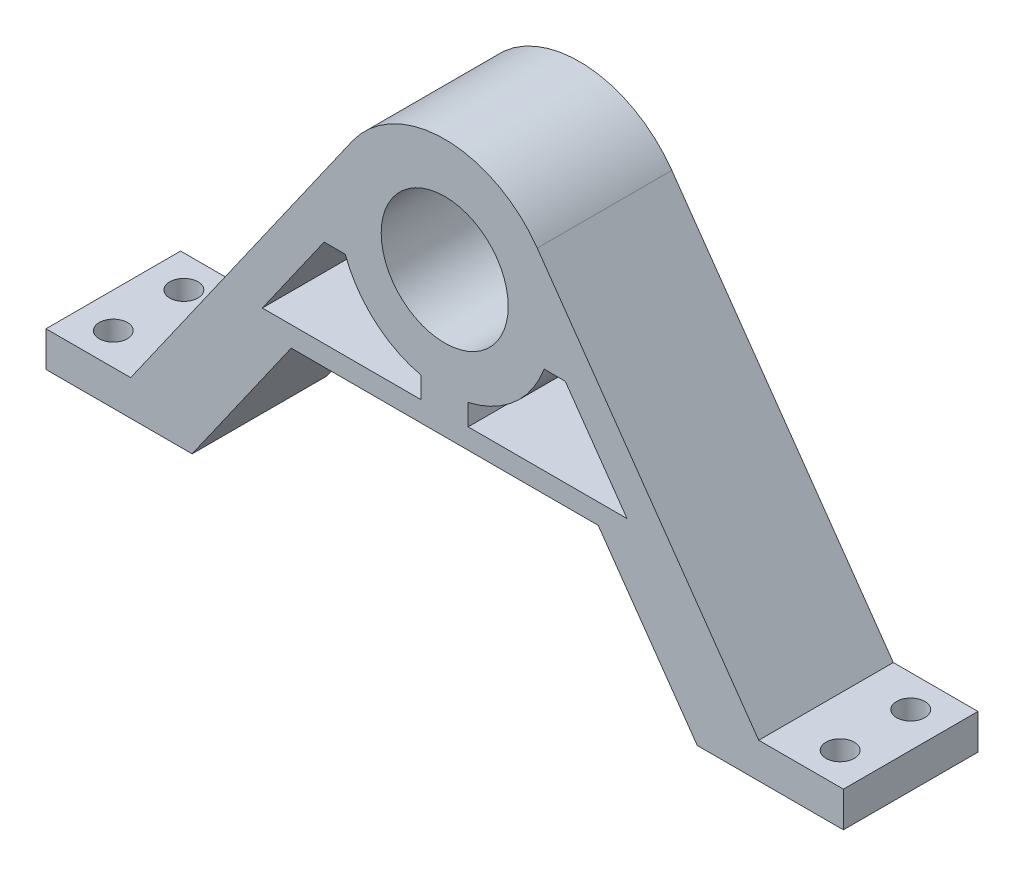
SolidWorks part; units mm, degrees
ref_plane "Plan de face" through (0, 0, 0) normal (0, 0, 1) x (1, 0, 0)
ref_plane "Plan de dessus" through (0, 0, 0) normal (0, 1, 0) x (1, 0, 0)
ref_plane "Plan de droite" through (0, 0, 0) normal (1, 0, 0) x (0, 0, -1)
sketch "Esquisse1" plane through (0, 0, 0) normal (0, 0, 1) x (1, 0, 0)
  line L0 (0, 0) -> (0, 20.2323) construction
  line L2 (-56.5, 0) -> (-56.5, 5)
  line L3 (-56.5, 5) -> (-44.5, 5)
  line L4 (-44.5, 5) -> (-44.5, 64.0193) construction
  line L11 (-56.5, 0) -> (-35.792, 0)
  line L28 (-13.1159, 49.7073) -> (-44.5, 5)
  line L29 (-35.792, 0) -> (-21.7522, 20)
  line L30 (35.792, 0) -> (21.7522, 20)
  line L31 (13.1159, 49.7073) -> (44.5, 5)
  line L32 (56.5, 0) -> (35.792, 0)
  line L33 (56.5, 5) -> (44.5, 5)
  line L34 (56.5, 0) -> (56.5, 5)
  line L35 (-21.7522, 20) -> (21.7522, 20)
  line L36 (-17.0873, 35.3475) -> (-25.8445, 22.8728)
  line L37 (-25.8445, 22.8728) -> (-3.3233, 22.8728)
  line L38 (-21.7522, 20) -> (-29.9368, 25.7456) construction
  line L39 (-3.3233, 22.8728) -> (-3.3233, 25.8728)
  line L40 (-17.0873, 35.3475) -> (-14.0873, 35.3475)
  line L41 (17.0873, 35.3475) -> (25.8445, 22.8728)
  line L42 (17.0873, 35.3475) -> (14.0873, 35.3475)
  line L43 (25.8445, 22.8728) -> (3.3233, 22.8728)
  line L44 (3.3233, 22.8728) -> (3.3233, 25.8728)
  circle A1 centre (0, 40.5) radius 11.025 construction
  arc A3 (13.1159, 49.7073) -> (-13.1159, 49.7073) centre (0, 40.5) ccw
  circle A4 centre (0, 40.5) radius 9
  arc A5 (-3.3233, 25.8728) -> (-14.0873, 35.3475) centre (0, 40.5) cw
  arc A6 (3.3233, 25.8728) -> (14.0873, 35.3475) centre (0, 40.5) ccw
  point P6 (0, 0)
  point P9 (-29.982, 25.6811)
  point P17 (0, 20)
  point P29 (0, 0)
  point P30 (0, 0)
  point P31 (0, 0)
  dimension "D1" = 22.05
  dimension "D5" = 5
  dimension "D9" = 18
  dimension "D10" = 15
  dimension "D2" = 40.5
  dimension "D3" = 5
  dimension "D4" = 12
  dimension "D6" = 10
  dimension "D7" = 113
  dimension "D8" = 20
  dimension "D11" = 3
extrude "Boss.-Extru.1" add sketch "Esquisse1" along normal blind 19.075
sketch "Esquisse2" plane through (0, 0, 0) normal (0, 0, -1) x (-1, 0, 0)
  circle A0 centre (0, 40.5) radius 11.025
  circle A1 centre (0, 40.5) radius 11.025 construction
extrude "Enlèv. mat.-Extru.1" cut sketch "Esquisse2" against normal blind 5.5
sketch "Esquisse6" plane through (0, 5, 0) normal (0, 1, 0) x (1, 0, 0)
  line L0 (-56.5, -9.5375) -> (56.5, -9.5375) construction
  line L1 (-56.5, -19.075) -> (-56.5, 0) construction
  line L2 (56.5, -19.075) -> (56.5, 0) construction
  line L3 (0, 0) -> (0, -19.075) construction
  line L4 (-13.1159, -19.075) -> (13.1159, -19.075) construction
  circle A0 centre (-51.5, -4.5375) radius 2
  circle A1 centre (51.5, -4.5375) radius 2
  circle A2 centre (51.5, -14.5375) radius 2
  circle A3 centre (-51.5, -14.5375) radius 2
  dimension "D1" = 5
  dimension "D3" = 4
  dimension "D2" = 5
extrude "Enlèv. mat.-Extru.5" cut sketch "Esquisse6" against normal through all
